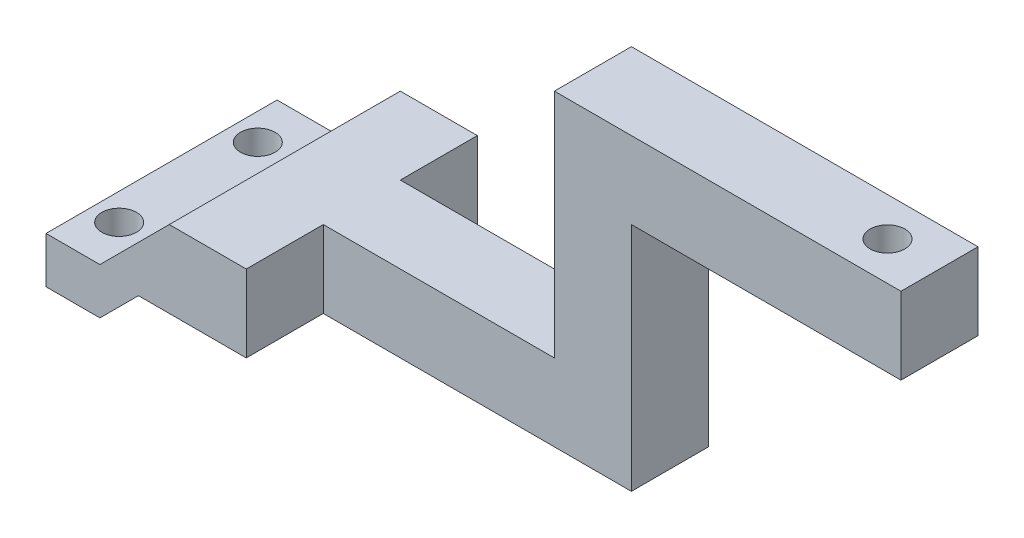
SolidWorks part; units mm, degrees
ref_plane "Front Plane" through (0, 0, 0) normal (0, 0, 1) x (1, 0, 0)
ref_plane "Top Plane" through (0, 0, 0) normal (0, 1, 0) x (1, 0, 0)
ref_plane "Right Plane" through (0, 0, 0) normal (1, 0, 0) x (0, 0, -1)
sketch "Sketch1" plane through (0, 0, 0) normal (0, 0, 1) x (1, 0, 0)
  line L0 (0, 0) -> (0, 6)
  line L1 (0, 6) -> (7, 6)
  line L2 (66, 5) -> (66, 35)
  line L3 (66, 35) -> (101, 35)
  line L4 (101, 35) -> (101, 45)
  line L5 (101, 45) -> (56, 45)
  line L6 (7, 6) -> (16, 15)
  line L7 (16, 15) -> (56, 15)
  line L8 (56, 45) -> (56, 15)
  line L9 (66, 5) -> (12, 5)
  line L10 (12, 5) -> (7, 0)
  line L11 (7, 0) -> (0, 0)
  dimension "D1" = 7
  dimension "D2" = 5
  dimension "D3" = 45
  dimension "D4" = 54
  dimension "D5" = 30
  dimension "D6" = 6
  dimension "D7" = 10
  dimension "D8" = 135
  dimension "D9" = 10
  dimension "D10" = 10
  dimension "D11" = 35
  dimension "D12" = 40
extrude "Boss-Extrude1" add sketch "Sketch1" along normal blind 30 contours L7 L8 L5 L4 L3 L2 L9 L10 L11 L0 L1 L6
sketch "Sketch2" plane through (0, 0, 30) normal (0, 0, 1) x (1, 0, 0)
  line L0 (26, 15) -> (26, 5)
  line L1 (16, 15) -> (56, 15) construction
  line L2 (66, 5) -> (12, 5) construction
  line L3 (26, 5) -> (66, 5)
  line L4 (66, 5) -> (66, 35)
  line L5 (66, 35) -> (101, 35)
  line L6 (101, 35) -> (101, 45)
  line L7 (101, 45) -> (56, 45)
  line L8 (56, 45) -> (56, 15)
  line L9 (56, 15) -> (26, 15)
  dimension "D1" = 40
extrude "Cut-Extrude1" cut sketch "Sketch2" against normal blind 10
sketch "Sketch4" plane through (0, 0, 0) normal (0, 0, -1) x (-1, 0, 0)
  line L0 (-66, 5) -> (-26, 5)
  line L1 (-66, 5) -> (-12, 5) construction
  line L2 (-26, 5) -> (-26, 15)
  line L3 (-16, 15) -> (-56, 15) construction
  line L4 (-26, 15) -> (-56, 15)
  line L5 (-56, 15) -> (-56, 45)
  line L6 (-56, 45) -> (-101, 45)
  line L7 (-101, 45) -> (-101, 35)
  line L8 (-101, 35) -> (-66, 35)
  line L9 (-66, 35) -> (-66, 5)
  dimension "D1" = 40
extrude "Cut-Extrude2" cut sketch "Sketch4" against normal blind 10
sketch "Sketch5" plane through (0, 45, 0) normal (0, 1, 0) x (1, 0, 0)
  line L0 (56, -10) -> (101, -10) construction
  circle A0 centre (94.2484, -15) radius 2.25
  dimension "D2" = 4.5
  dimension "D1" = 5
extrude "Cut-Extrude3" cut sketch "Sketch5" against normal through all
sketch "Sketch6" plane through (0, 6, 0) normal (0, 1, 0) x (1, 0, 0)
  line L0 (0, -15) -> (-15.1482, -15) construction
  line L1 (0, -30) -> (0, 0) construction
  line L2 (3.5, 0) -> (3.5, -30) construction
  line L3 (0, 0) -> (7, 0) construction
  line L4 (0, -30) -> (7, -30) construction
  circle A0 centre (3.5, -6) radius 2.25
  circle A1 centre (3.5, -24) radius 2.25
  dimension "D1" = 4.5
  dimension "D4" = 4.5
  dimension "D2" = 9
  dimension "D3" = 9
extrude "Cut-Extrude4" cut sketch "Sketch6" against normal blind 10
